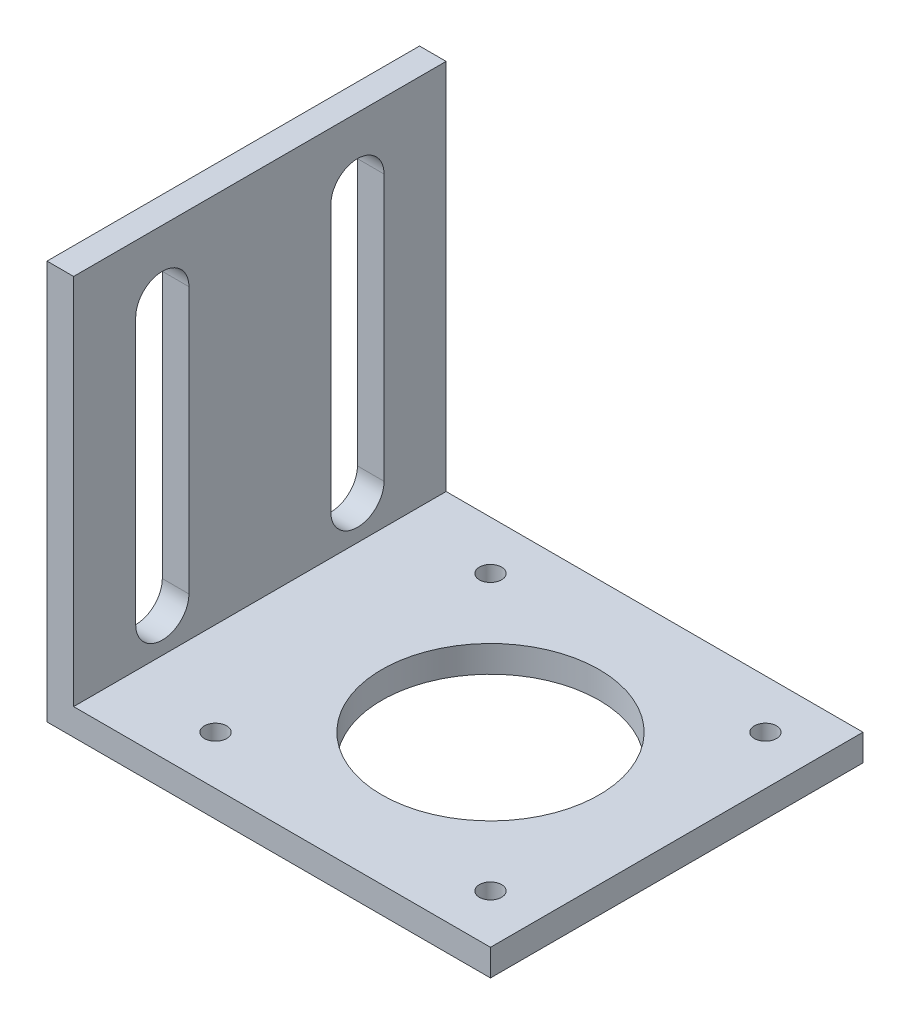
SolidWorks part; units mm, degrees
ref_plane "Front Plane" through (0, 0, 0) normal (0, 0, 1) x (1, 0, 0)
ref_plane "Top Plane" through (0, 0, 0) normal (0, 1, 0) x (1, 0, 0)
ref_plane "Right Plane" through (0, 0, 0) normal (1, 0, 0) x (0, 0, -1)
sketch "Sketch1" plane through (0, 0, 0) normal (0, 1, 0) x (1, 0, 0)
  line L1 (-25, 21) -> (25, 21)
  line L2 (-25, 21) -> (-25, -21)
  line L3 (-25, -21) -> (25, -21)
  line L4 (25, 21) -> (25, -21)
  line L5 (-25, 21) -> (25, -21) construction
  line L6 (-25, -21) -> (25, 21) construction
  point P0 (0, 0)
  dimension "D1" = 50
  dimension "D2" = 42
extrude "Boss-Extrude1" add sketch "Sketch1" along normal blind 3
sketch "Sketch2" plane through (0, 3, 0) normal (0, 1, 0) x (1, 0, 0)
  line L0 (-25, -21) -> (25, -21) construction
  line L1 (-25, 21) -> (-22, 21)
  line L2 (-25, 21) -> (-25, -21)
  line L3 (-25, -21) -> (-22, -21)
  line L4 (-22, 21) -> (-22, -21)
  dimension "D1" = 3
extrude "Boss-Extrude2" add sketch "Sketch2" along normal blind 42
sketch "Sketch4" plane through (-25, 0, 0) normal (-1, 0, 0) x (0, 0, 1)
  line L0 (-11, 0) -> (-11, 45) construction
  line L1 (-21, 0) -> (21, 0) construction
  line L2 (-21, 45) -> (21, 45) construction
  line L3 (11, 0) -> (11, 45) construction
  line L4 (-21, 45) -> (-21, 0) construction
  line L6 (21, 45) -> (21, 0) construction
  line L8 (-14, 7.5) -> (-8, 7.5)
  line L9 (-14, 7.5) -> (-14, 37.5)
  line L10 (-14, 37.5) -> (-8, 37.5)
  line L11 (-8, 7.5) -> (-8, 37.5)
  line L12 (-14, 7.5) -> (-8, 37.5) construction
  line L13 (-14, 37.5) -> (-8, 7.5) construction
  line L14 (8, 7.5) -> (14, 7.5)
  line L15 (8, 7.5) -> (8, 37.5)
  line L16 (8, 37.5) -> (14, 37.5)
  line L17 (14, 7.5) -> (14, 37.5)
  line L18 (8, 7.5) -> (14, 37.5) construction
  line L19 (8, 37.5) -> (14, 7.5) construction
  circle A1 centre (-11, 7.5) radius 3
  circle A2 centre (-11, 37.5) radius 3
  circle A3 centre (11, 7.5) radius 3
  circle A4 centre (11, 37.5) radius 3
  point P15 (-11, 22.5)
  point P20 (11, 22.5)
  dimension "D4" = 6
  dimension "D5" = 6
  dimension "D1" = 10
  dimension "D2" = 10
  dimension "D3" = 30
  dimension "D6" = 30
extrude "Cut-Extrude2" cut sketch "Sketch4" against normal blind 10 contours L8 A1 | L8 A1 | A2 L9 A1 L11 | L10 A2 | L10 A2 | A4 L15 A3 L17 | L16 A4 | L16 A4 | L14 A3 | L14 A3
sketch "Sketch5" plane through (0, 3, 0) normal (0, 1, 0) x (1, 0, 0)
  circle A0 centre (4, 0) radius 12.25
  circle A1 centre (-11.5, -15.5) radius 1.25
  circle A2 centre (19.5, -15.5) radius 1.25
  circle A3 centre (19.5, 15.5) radius 1.25
  circle A4 centre (-11.5, 15.5) radius 1.25
extrude "Cut-Extrude3" cut sketch "Sketch5" against normal blind 10
